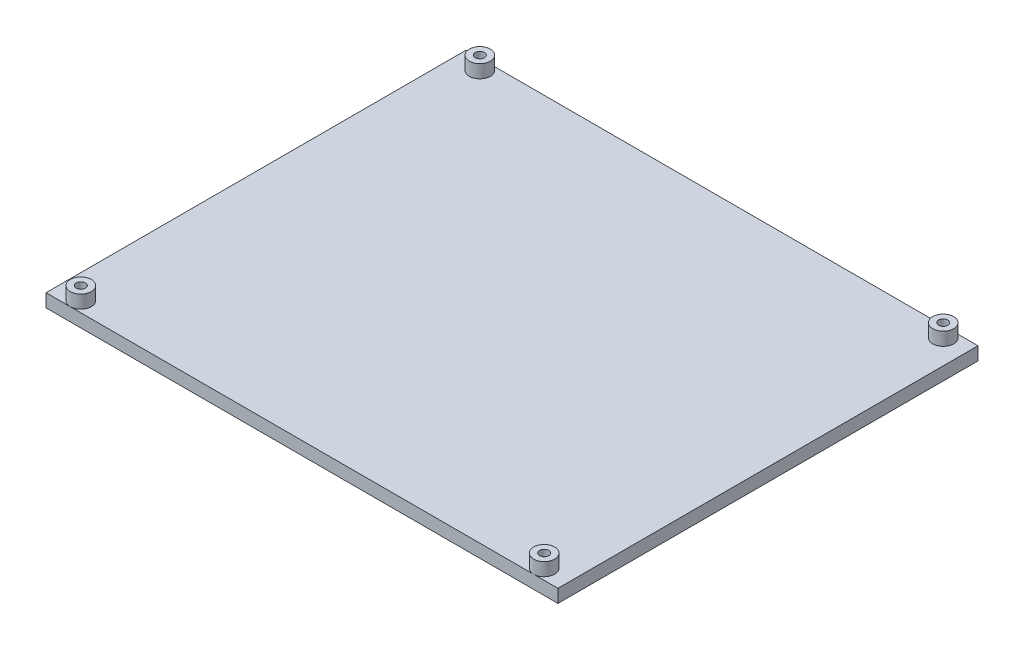
SolidWorks part; units mm, degrees
ref_plane "Front Plane" through (0, 0, 0) normal (0, 0, 1) x (1, 0, 0)
ref_plane "Top Plane" through (0, 0, 0) normal (0, 1, 0) x (1, 0, 0)
ref_plane "Right Plane" through (0, 0, 0) normal (1, 0, 0) x (0, 0, -1)
sketch "Sketch1" plane through (0, 0, 0) normal (0, 1, 0) x (1, 0, 0)
  line L1 (-88.25, -76) -> (88.25, -76) construction
  line L2 (-88.25, -76) -> (-88.25, 76) construction
  line L3 (-88.25, 76) -> (88.25, 76) construction
  line L4 (88.25, -76) -> (88.25, 76) construction
  line L5 (-88.25, -76) -> (88.25, 76) construction
  line L6 (-88.25, 76) -> (88.25, -76) construction
  line L7 (-92.5, -80) -> (92.5, -80)
  line L8 (-92.5, -80) -> (-92.5, 80) construction
  line L9 (-92.5, 80) -> (92.5, 80)
  line L10 (92.5, -80) -> (92.5, 80) construction
  line L11 (-92.5, -80) -> (92.5, 80) construction
  line L12 (-92.5, 80) -> (92.5, -80) construction
  line L13 (92.5, -80) -> (97.5, -80)
  line L15 (92.5, 80) -> (97.5, 80)
  line L16 (97.5, -80) -> (97.5, 80)
  line L17 (-92.5, -80) -> (-97.5, -80)
  line L19 (-92.5, 80) -> (-97.5, 80)
  line L20 (-97.5, -80) -> (-97.5, 80)
  circle A0 centre (-88.25, 76) radius 1.75
  circle A1 centre (88.25, 76) radius 1.75
  circle A2 centre (88.25, -76) radius 1.75
  circle A3 centre (-88.25, -76) radius 1.75
  point P0 (0, 0)
  point P6 (0, 0)
  point P19 (92.5, 78.5777)
  point P21 (0, 0)
  point P22 (0, 0)
  point P23 (-92.5, 78.3548)
  dimension "D5" = 3.5
  dimension "D1" = 176.5
  dimension "D2" = 152
  dimension "D3" = 185
  dimension "D4" = 160
  dimension "D6" = 5
extrude "Boss-Extrude1" add sketch "Sketch1" along normal blind 5
sketch "Sketch2" plane through (0, 5, 0) normal (0, 1, 0) x (1, 0, 0)
  circle A0 centre (-88.25, 76) radius 4
  circle A1 centre (88.25, 76) radius 4
  circle A2 centre (88.25, -76) radius 4
  circle A3 centre (-88.25, -76) radius 4
  circle A4 centre (-88.25, -76) radius 1.75 construction
  circle A5 centre (88.25, -76) radius 1.75 construction
  circle A6 centre (88.25, 76) radius 1.75 construction
  circle A7 centre (-88.25, 76) radius 1.75 construction
  circle A8 centre (-88.25, -76) radius 1.75
  circle A9 centre (88.25, -76) radius 1.75
  circle A10 centre (88.25, 76) radius 1.75
  circle A11 centre (-88.25, 76) radius 1.75
  dimension "D1" = 8
extrude "Boss-Extrude2" add sketch "Sketch2" along normal blind 5
